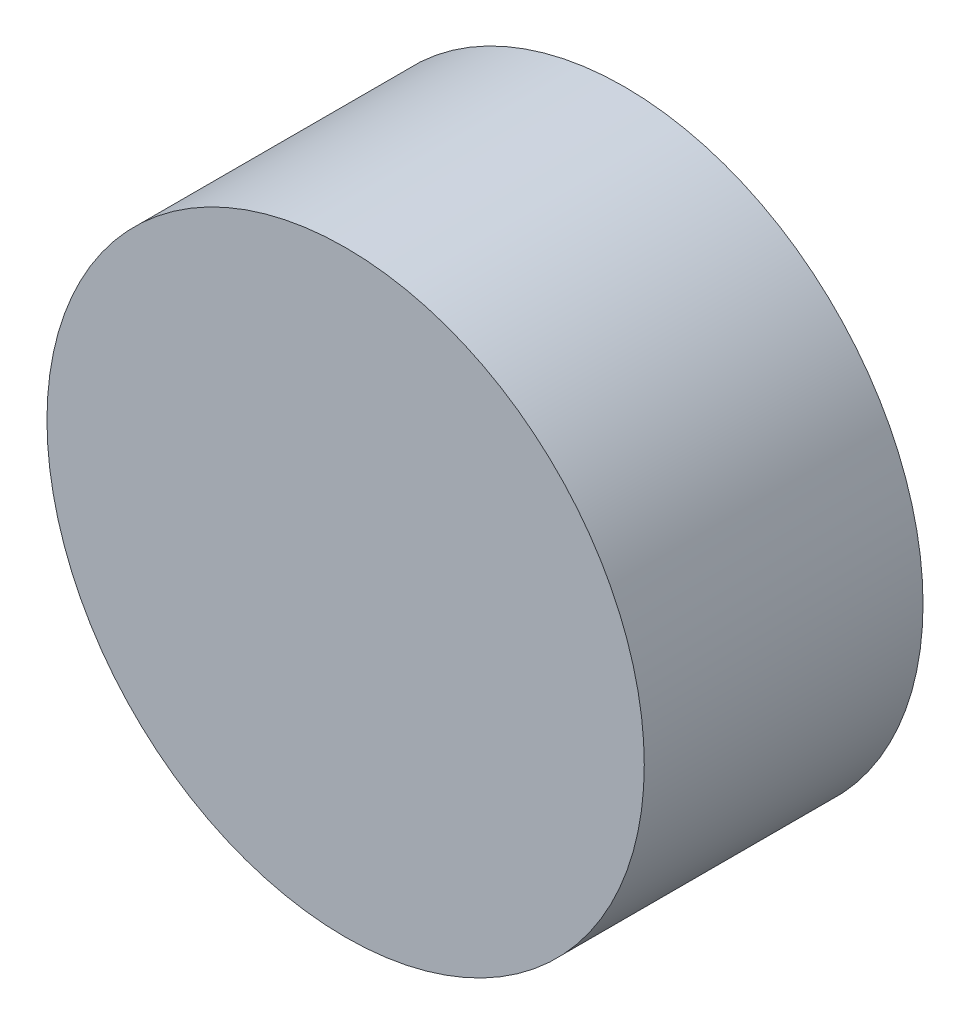
SolidWorks part; units mm, degrees
ref_plane "Front" through (0, 0, 0) normal (0, 0, 1) x (1, 0, 0)
ref_plane "Top" through (0, 0, 0) normal (0, 1, 0) x (1, 0, 0)
ref_plane "Right" through (0, 0, 0) normal (1, 0, 0) x (0, 0, -1)
sketch "Sketch1" plane through (0, 0, 0) normal (0, 0, 1) x (1, 0, 0)
  circle A0 centre (0, 0) radius 9.525
  dimension "D1" = 19.05
extrude "Boss-Extrude1" add sketch "Sketch1" along normal blind 8.89
